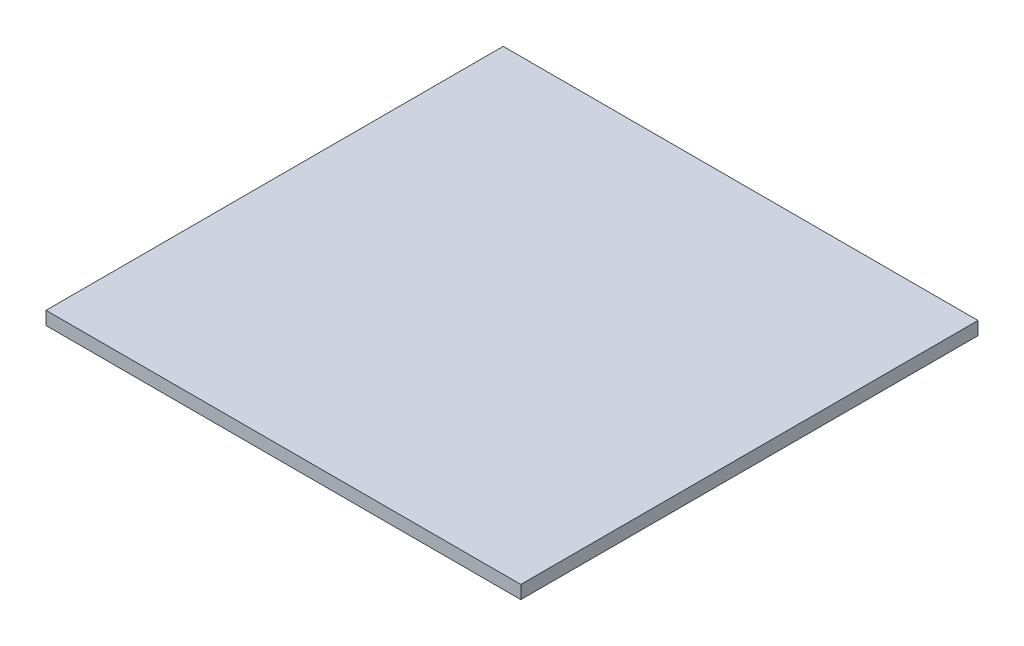
SolidWorks part; units mm, degrees
ref_plane "Front Plane" through (0, 0, 0) normal (0, 0, 1) x (1, 0, 0)
ref_plane "Top Plane" through (0, 0, 0) normal (0, 1, 0) x (1, 0, 0)
ref_plane "Right Plane" through (0, 0, 0) normal (1, 0, 0) x (0, 0, -1)
sketch "Sketch1" plane through (0, 0, 0) normal (0, 1, 0) x (1, 0, 0)
  line L1 (0, 0) -> (171.45, 0)
  line L2 (0, 0) -> (0, -165.1)
  line L3 (0, -165.1) -> (171.45, -165.1)
  line L4 (171.45, 0) -> (171.45, -165.1)
  dimension "D1" = 165.1
  dimension "D2" = 171.45
extrude "Boss-Extrude1" add sketch "Sketch1" along normal blind 4.7625 contours L1 L4 L3 L2
